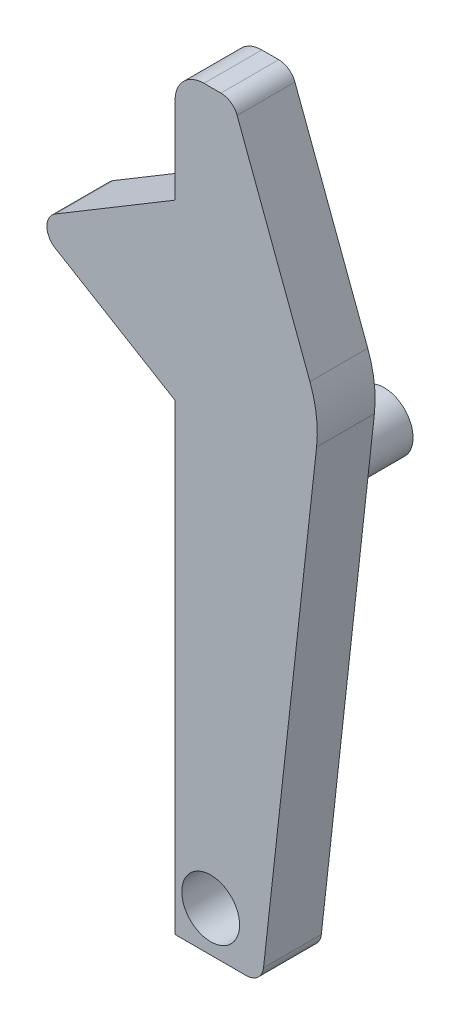
SolidWorks part; units mm, degrees
ref_plane "Alzado" through (0, 0, 0) normal (0, 0, 1) x (1, 0, 0)
ref_plane "Planta" through (0, 0, 0) normal (0, 1, 0) x (1, 0, 0)
ref_plane "Vista lateral" through (0, 0, 0) normal (1, 0, 0) x (0, 0, -1)
sketch "Croquis1" plane through (0, 0, 0) normal (0, 0, 1) x (1, 0, 0)
  line L0 (0.3068, 2.0299) -> (0.9363, 0.3511)
  line L1 (0.9939, -0.1104) -> (0.5351, -4.2393)
  line L2 (-0.2297, 1.8772) -> (-0.2297, 1.1272)
  line L3 (-0.2297, 1.1272) -> (-1.2653, 0.5059)
  line L4 (0.386, -4.3728) -> (-0.2297, -4.3728)
  line L5 (-1.2653, 0.2486) -> (-0.2297, -0.3728)
  line L6 (-0.2297, -0.3728) -> (-0.2297, -4.3728)
  line L8 (0.1663, 2.1272) -> (0.0203, 2.1272)
  arc A0 (0.5351, -4.2393) -> (0.386, -4.3728) centre (0.386, -4.2228) cw
  arc A1 (0.3068, 2.0299) -> (0.1663, 2.1272) centre (0.1663, 1.9772) ccw
  arc A2 (0.9363, 0.3511) -> (0.9939, -0.1104) centre (0, 0) cw
  arc A3 (-1.2653, 0.5059) -> (-1.2653, 0.2486) centre (-1.1882, 0.3772) ccw
  arc A4 (0.0203, 2.1272) -> (-0.2297, 1.8772) centre (0.0203, 1.8772) ccw
  point P8 (0.5203, -4.3728)
  point P11 (0.2703, 2.1272)
  point P15 (1.0203, 0.1272)
  point P18 (-1.4797, 0.3772)
  point P23 (-0.2297, 2.1272)
  dimension "D7" = 0.75
  dimension "D8" = 1
  dimension "D9" = 1.25
  dimension "D10" = 0.15
  dimension "D11" = 1
  dimension "D12" = 0.15
  dimension "D13" = 0.25
  dimension "D1" = 6.5
  dimension "D2" = 0.5
  dimension "D3" = 0.75
  dimension "D4" = 0.75
  dimension "D5" = 1.25
  dimension "D6" = 2
extrude "Saliente-Extruir1" add sketch "Croquis1" along normal blind 0.5
sketch "Croquis2" plane through (0, 0, 0) normal (0, 0, -1) x (-1, 0, 0)
  line L0 (0.2297, -4.3728) -> (-0.386, -4.3728) construction
  circle A0 centre (-0.0782, -4.0228) radius 0.25
  point P4 (-0.0782, -4.3728)
  dimension "D2" = 0.5
  dimension "D1" = 0.35
sketch "Croquis3" plane through (0, 0, 0) normal (0, 0, -1) x (-1, 0, 0)
  line L1 (-0.0782, -1.1228) -> (-0.0782, -4.3728) construction
  line L2 (0.2297, -4.3728) -> (-0.386, -4.3728) construction
  line L3 (0.2297, -0.3728) -> (0.2297, -4.3728) construction
  circle A0 centre (-0.0782, -1.1228) radius 0.25
  point P5 (-0.0782, -4.3728)
  dimension "D1" = 3.25
extrude "Saliente-Extruir3" add sketch "Croquis3" along normal blind 1
extrude "Cortar-Extruir1" cut sketch "Croquis2" against normal up to next
